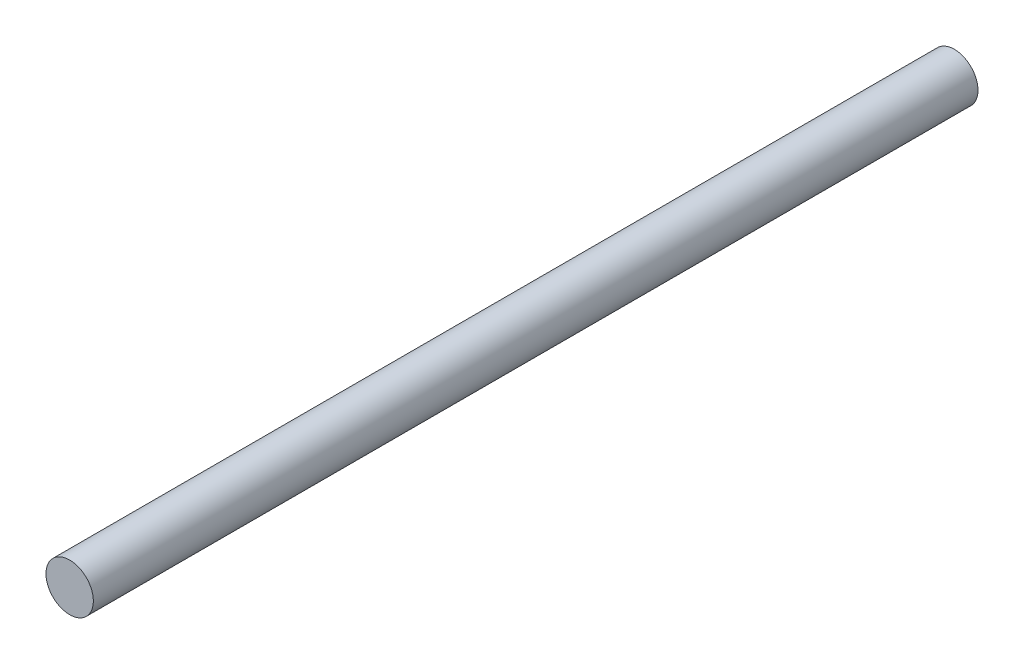
SolidWorks part; units mm, degrees
ref_plane "Front Plane" through (0, 0, 0) normal (0, 0, 1) x (1, 0, 0)
ref_plane "Top Plane" through (0, 0, 0) normal (0, 1, 0) x (1, 0, 0)
ref_plane "Right Plane" through (0, 0, 0) normal (1, 0, 0) x (0, 0, -1)
sketch "Sketch1" plane through (0, 0, 0) normal (0, 0, 1) x (1, 0, 0)
  circle A0 centre (0, 0) radius 15
  dimension "D1" = 30
extrude "Boss-Extrude1" add sketch "Sketch1" along normal blind 560
